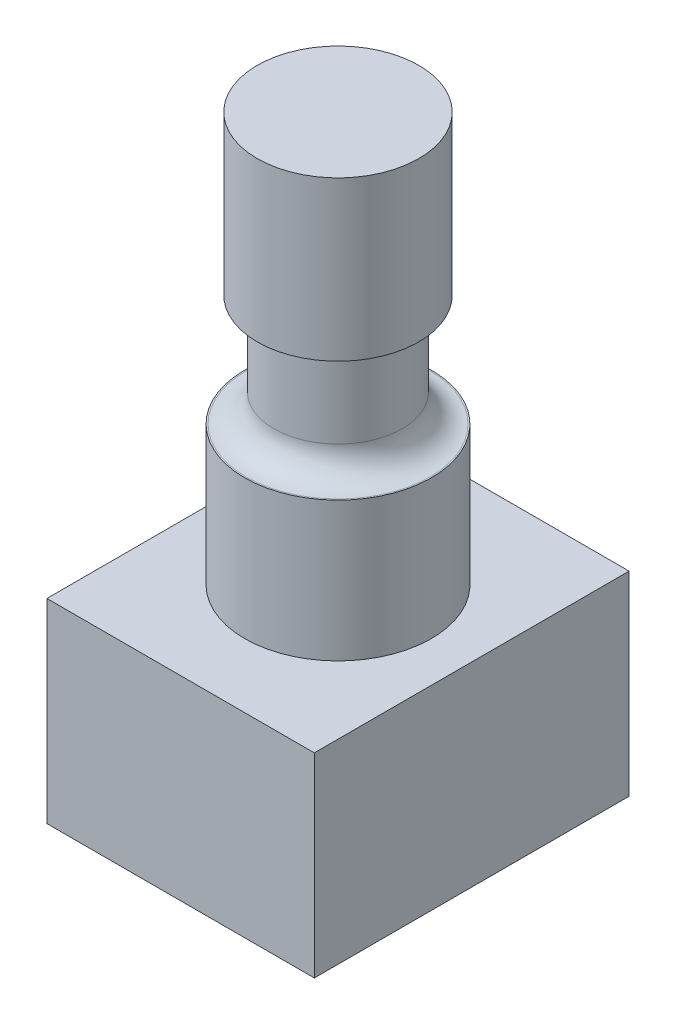
SolidWorks part; units mm, degrees
ref_plane "Спереди" through (0, 0, 0) normal (0, 0, 1) x (1, 0, 0)
ref_plane "Сверху" through (0, 0, 0) normal (0, 1, 0) x (1, 0, 0)
ref_plane "Справа" through (0, 0, 0) normal (1, 0, 0) x (0, 0, -1)
sketch "Sketch1" plane through (0, 0, 0) normal (0, 1, 0) x (1, 0, 0)
  line L1 (4.8, -5.65) -> (-4.8, -5.65)
  line L2 (4.8, -5.65) -> (4.8, 5.65)
  line L3 (4.8, 5.65) -> (-4.8, 5.65)
  line L4 (-4.8, -5.65) -> (-4.8, 5.65)
  line L5 (4.8, -5.65) -> (-4.8, 5.65) construction
  line L6 (4.8, 5.65) -> (-4.8, -5.65) construction
  point P0 (0, 0)
  dimension "D1" = 9.6
  dimension "D2" = 11.3
extrude "Boss-Extrude1" add sketch "Sketch1" along normal blind 7
sketch "Sketch2" plane through (0, 7, 0) normal (0, 1, 0) x (1, 0, 0)
  circle A0 centre (0, 0) radius 3.35
  dimension "D1" = 6.7
extrude "Boss-Extrude2" add sketch "Sketch2" along normal blind 5
sketch "Sketch3" plane through (0, 12, 0) normal (0, 1, 0) x (1, 0, 0)
  circle A0 centre (0, 0) radius 2.3
  dimension "D1" = 4.6
extrude "Boss-Extrude3" add sketch "Sketch3" along normal blind 4
fillet "Fillet1" radius 1 1 edges at (0, 12, 2.3)
sketch "Sketch4" plane through (0, 16, 0) normal (0, 1, 0) x (1, 0, 0)
  circle A0 centre (0, 0) radius 2.9
  dimension "D1" = 5.8
extrude "Boss-Extrude4" add sketch "Sketch4" along normal blind 5.7
